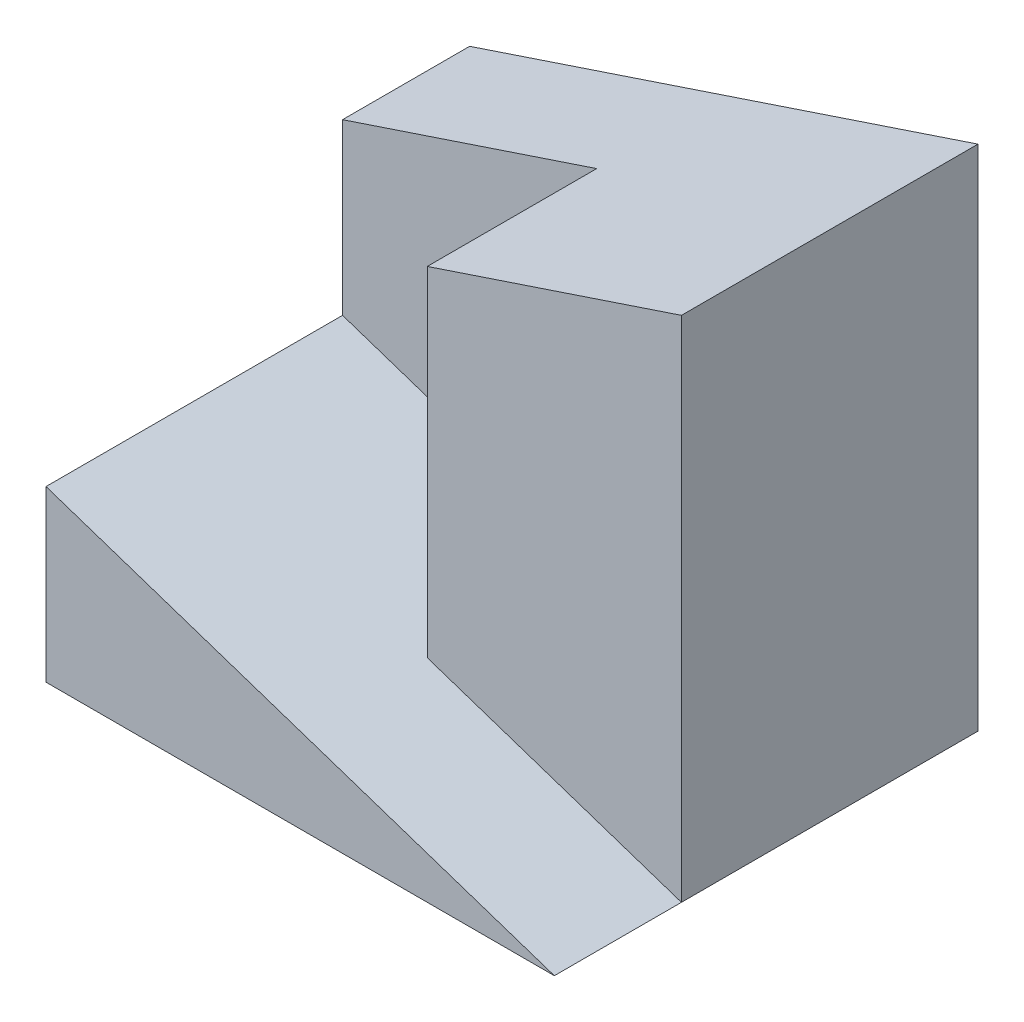
SolidWorks part; units mm, degrees
ref_plane "Front Plane" through (0, 0, 0) normal (0, 0, 1) x (1, 0, 0)
ref_plane "Top Plane" through (0, 0, 0) normal (0, 1, 0) x (1, 0, 0)
ref_plane "Right Plane" through (0, 0, 0) normal (1, 0, 0) x (0, 0, -1)
sketch "Sketch1" plane through (0, 0, 0) normal (0, 1, 0) x (1, 0, 0)
  line L1 (-3, -2.5) -> (3, -2.5)
  line L2 (-3, -2.5) -> (-3, 2.5)
  line L3 (-3, 2.5) -> (3, 2.5)
  line L4 (3, -2.5) -> (3, 2.5)
  line L5 (-3, -2.5) -> (3, 2.5) construction
  line L6 (-3, 2.5) -> (3, -2.5) construction
  point P0 (0, 0)
  dimension "D1" = 5
  dimension "D2" = 6
extrude "Boss-Extrude1" add sketch "Sketch1" along normal blind 6
sketch "Sketch2" plane through (0, 0, 2.5) normal (0, 0, 1) x (1, 0, 0)
  line L0 (-3, 2) -> (3, 0)
  line L1 (-3, 6) -> (-3, 0) construction
  line L2 (3, 0) -> (3, 6)
  line L3 (3, 6) -> (-3, 6)
  line L4 (-3, 6) -> (-3, 2)
  line L5 (0, 6) -> (0, 1)
  line M4 (-3, 6) -> (-3, 0)
  dimension "D1" = 2
extrude "Cut-Extrude1" cut sketch "Sketch2" against normal blind 3.5 contours L5 L3 L0 M4
sketch "Sketch3" plane through (0, 0, 2.5) normal (0, 0, 1) x (1, 0, 0)
  line L0 (0, 1) -> (3, 0)
  line L1 (3, 0) -> (3, 6)
  line L2 (3, 6) -> (0, 6)
  line L3 (0, 6) -> (0, 1)
extrude "Cut-Extrude2" cut sketch "Sketch3" against normal blind 1.5
sketch "Sketch4" plane through (0, 0, 1) normal (0, 0, 1) x (1, 0, 0)
  line L0 (3, 6) -> (-3, 4)
  line L1 (-3, 6) -> (-3, 2) construction
  line L2 (-3, 4) -> (-3, 6)
  line L3 (-3, 6) -> (3, 6)
  dimension "D1" = 2
extrude "Cut-Extrude3" cut sketch "Sketch4" against normal blind 11.5
